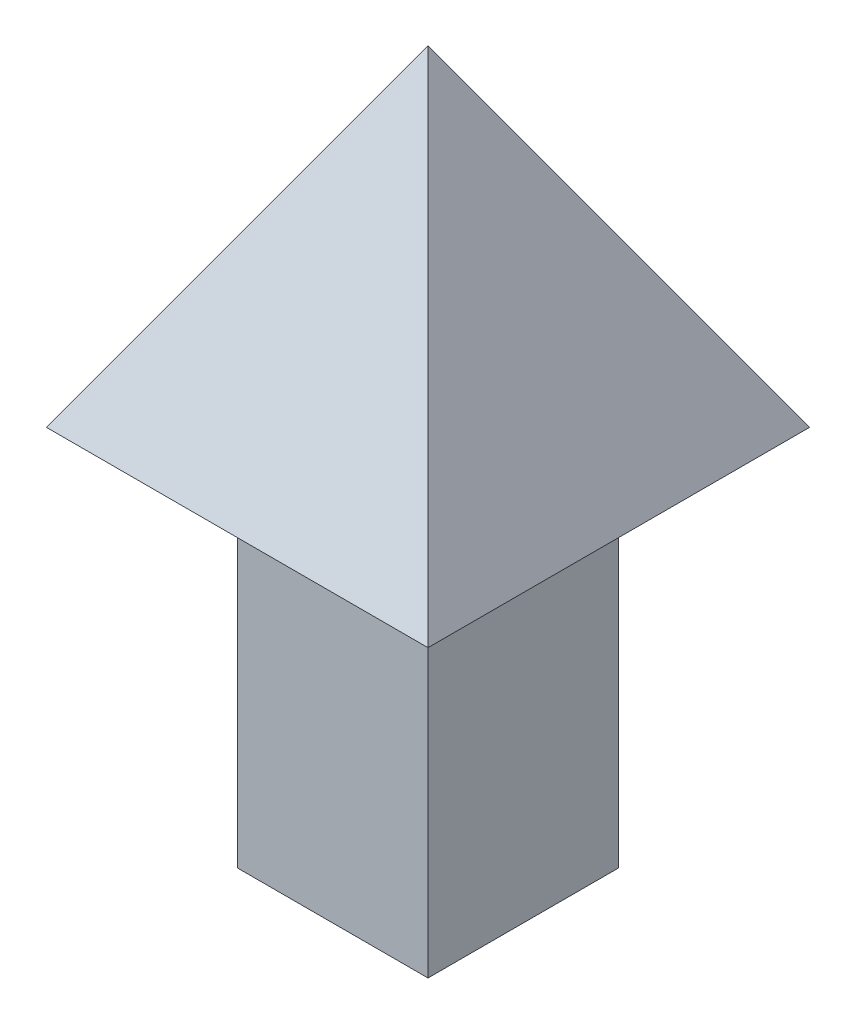
SolidWorks part; units mm, degrees
ref_plane "Front Plane" through (0, 0, 0) normal (0, 0, 1) x (1, 0, 0)
ref_plane "Top Plane" through (0, 0, 0) normal (0, 1, 0) x (1, 0, 0)
ref_plane "Right Plane" through (0, 0, 0) normal (1, 0, 0) x (0, 0, -1)
sketch "Sketch1" plane through (0, 0, 0) normal (0, 1, 0) x (1, 0, 0)
  line L0 (500, 500) -> (-500, -500) construction
  line L1 (-500, -500) -> (500, -500)
  line L2 (-500, -500) -> (-500, 500)
  line L3 (-500, 500) -> (500, 500)
  line L4 (500, -500) -> (500, 500)
  point P4 (500, -673.8792)
  point P5 (0, 0)
  dimension "D1" = 1000
  dimension "D2" = 1000
extrude "Boss-Extrude1" add sketch "Sketch1" along normal blind 2000
sketch "Sketch4" plane through (0, 2000, 0) normal (0, 1, 0) x (1, 0, 0)
  line L0 (1000, 1000) -> (-1000, -1000) construction
  line L1 (-1000, -1000) -> (1000, -1000)
  line L2 (-1000, -1000) -> (-1000, 1000)
  line L3 (-1000, 1000) -> (1000, 1000)
  line L4 (1000, -1000) -> (1000, 1000)
  line L5 (500, 466.9287) -> (500, 500) construction
  line L6 (500, -500) -> (500, 500) construction
  line L7 (500, 500) -> (-500, -500) construction
  line L8 (-500, -500) -> (500, -500) construction
  point P9 (0, 0)
  dimension "D1" = 500
  dimension "D2" = 500
extrude "Boss-Extrude3" add sketch "Sketch4" along normal blind 2000 draft 30
